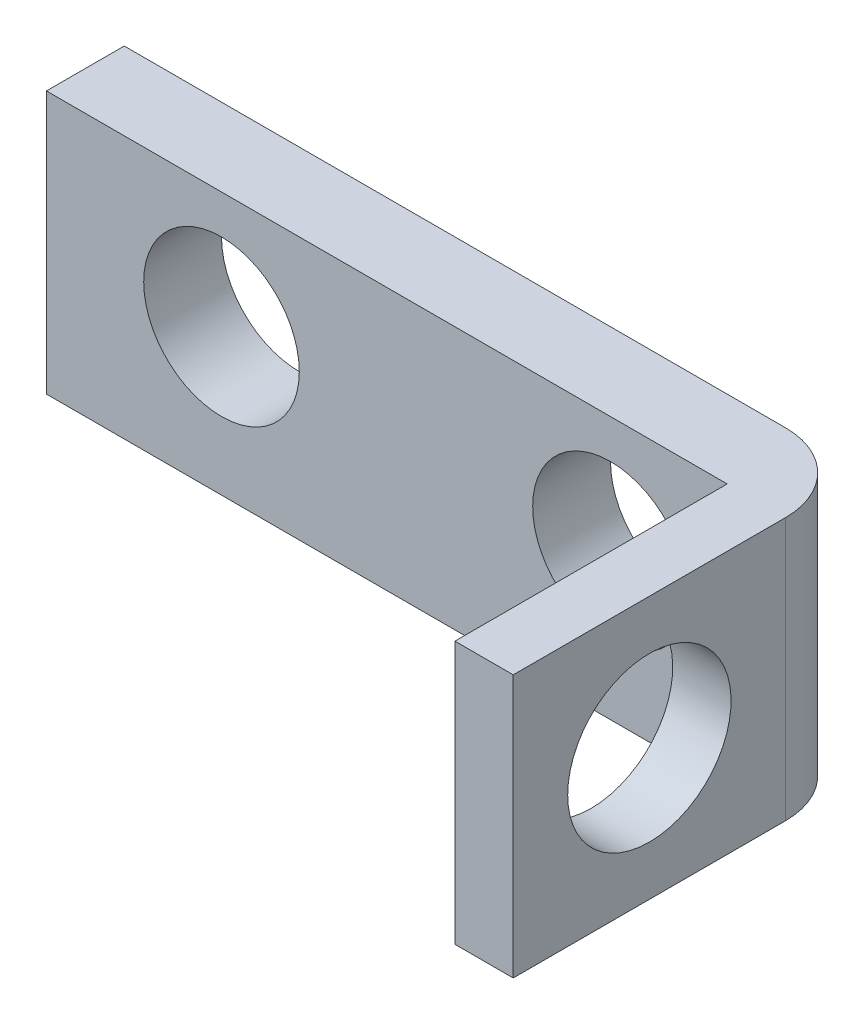
SolidWorks part; units mm, degrees
ref_plane "Plan de face" through (0, 0, 0) normal (0, 0, 1) x (1, 0, 0)
ref_plane "Plan de dessus" through (0, 0, 0) normal (0, 1, 0) x (1, 0, 0)
ref_plane "Plan de droite" through (0, 0, 0) normal (1, 0, 0) x (0, 0, -1)
sketch "Esquisse1" plane through (0, 0, 0) normal (0, 0, 1) x (1, 0, 0)
  line L1 (0, 0) -> (19, 0)
  line L2 (0, 0) -> (0, -6.75)
  line L3 (0, -6.75) -> (19, -6.75)
  line L4 (19, 0) -> (19, -6.75)
  dimension "D1" = 6.75
  dimension "D2" = 19
extrude "Boss.-Extru.1" add sketch "Esquisse1" along normal blind 2
sketch "Esquisse2" plane through (0, 0, 0) normal (0, 0, -1) x (-1, 0, 0)
  line L0 (-9.5, 0) -> (-9.5, -6.75) construction
sketch "Esquisse4" plane through (0, 0, 0) normal (0, 0, -1) x (-1, 0, 0)
  circle A0 centre (-14.5, -3) radius 2
  circle A1 centre (-4.5, -3) radius 2
extrude "Enlèv. mat.-Extru.1" cut sketch "Esquisse4" against normal blind 10
ref_plane "Plan1" through (0, 0, 27) normal (0, 0, -1) x (-1, 0, 0)
sketch "Esquisse6" plane through (0, 0, 2) normal (0, 0, 1) x (1, 0, 0)
  line L0 (19, -6.75) -> (19, 0) construction
  line L1 (19, 0) -> (17.5, 0)
  line L2 (19, 0) -> (19, -6.75)
  line L3 (19, -6.75) -> (17.5, -6.75)
  line L4 (17.5, 0) -> (17.5, -6.75)
  dimension "D1" = 1.5
extrude "Boss.-Extru.2" add sketch "Esquisse6" along normal blind 7
fillet "Congé1" radius 2 1 edges at (19, -3.375, 0)
sketch "Esquisse7" plane through (17.5, 0, 0) normal (-1, 0, 0) x (0, 0, 1)
  line L0 (9, 0) -> (2, -6.75) construction
  circle A0 centre (5.5, -3.375) radius 2.1
  dimension "D1" = 4.2
extrude "Enlèv. mat.-Extru.2" cut sketch "Esquisse7" against normal blind 3
